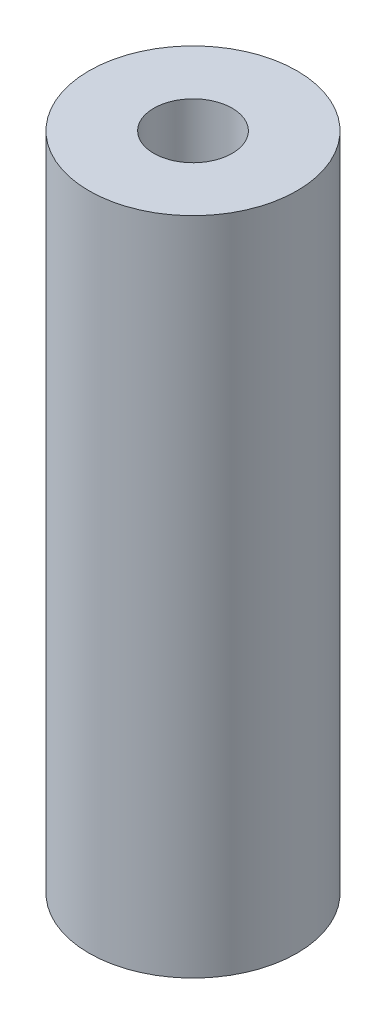
SolidWorks part; units mm, degrees
material "6061-T6 (SS)"
ref_plane "Front Plane" through (0, 0, 0) normal (0, 0, 1) x (1, 0, 0)
ref_plane "Top Plane" through (0, 0, 0) normal (0, 1, 0) x (1, 0, 0)
ref_plane "Right Plane" through (0, 0, 0) normal (1, 0, 0) x (0, 0, -1)
sketch "Sketch1" plane through (0, 0, 0) normal (0, 1, 0) x (1, 0, 0)
  circle A0 centre (0, 0) radius 3
  circle A1 centre (0, 0) radius 3
  dimension "D1" = 6
  dimension "D2" = 6
extrude "Boss-Extrude1" add sketch "Sketch1" along normal blind 19.05 contours A0
hole_wizard "#4-40 Tapped Hole1" positions "Sketch2" profile "Sketch3" tap size "#4-40" standard "ANSI Inch" end condition through all
sketch "Sketch2" plane through (0, 0, 0) normal (0, -1, 0) x (-1, 0, 0)
  point P0 (0, 0)
sketch "Sketch3" plane through (0, 0, 0) normal (1, 0, 0) x (0, 0, -1)
  line L0 (0, 0) -> (0, 19.05)
  line L1 (0, 19.05) -> (1.1303, 19.05)
  line L2 (1.1303, 19.05) -> (1.1303, 0)
  line L5 (1.1303, 0) -> (0, 0)
  line L11 (0, -6.35) -> (0, 107.95) construction
  dimension "Thread Major Dia." = 2.2606
  dimension "Thru Tap Drill Depth" = 19.05
hole_wizard "M2.5x0.45 Tapped Hole1" positions "Sketch4" profile "Sketch5" tap size "M2.5x0.45" standard "ANSI Metric"
sketch "Sketch4" plane through (0, 0, 0) normal (0, -1, 0) x (-1, 0, 0)
  point P0 (0, 0)
sketch "Sketch5" plane through (0, 0, 0) normal (1, 0, 0) x (0, 0, -1)
  line L0 (0, 0) -> (0, 11)
  line L1 (0, 11) -> (1.025, 11)
  line L2 (1.025, 11) -> (1.025, 0)
  line L5 (1.025, 0) -> (0, 0)
  line L11 (0, -6.35) -> (0, 107.95) construction
  dimension "Thread Major Dia." = 2.05
  dimension "Thru Tap Drill Depth" = 11
